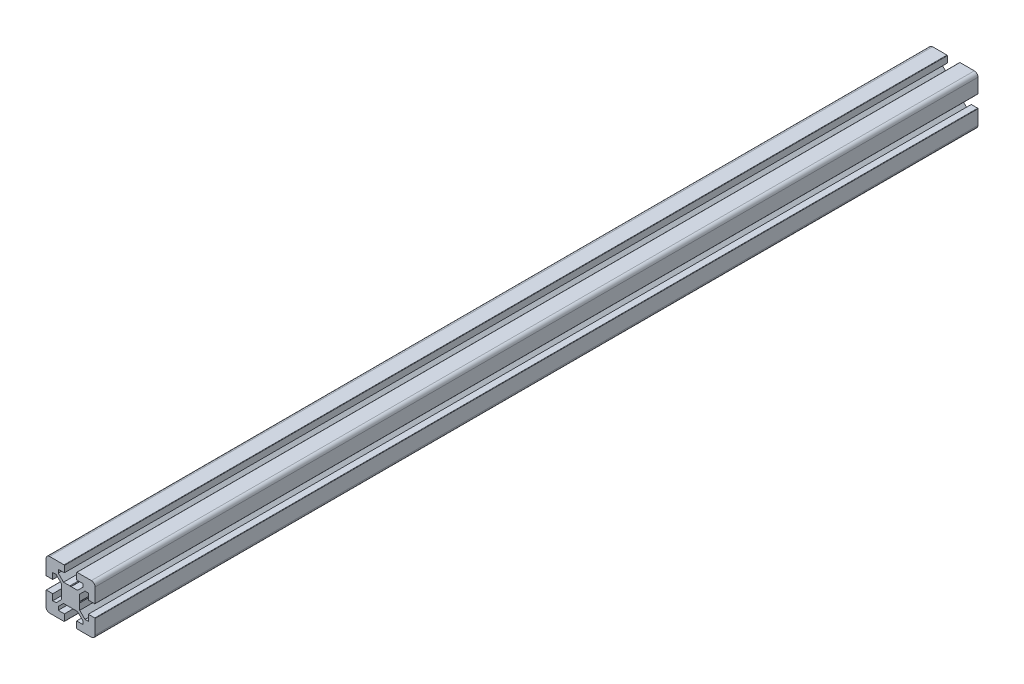
SolidWorks part; units mm, degrees
ref_plane "正面" through (0, 0, 0) normal (0, 0, 1) x (1, 0, 0)
ref_plane "平面" through (0, 0, 0) normal (0, 1, 0) x (1, 0, 0)
ref_plane "右側面" through (0, 0, 0) normal (1, 0, 0) x (0, 0, -1)
sketch "Model" plane through (0, 0, 0) normal (0, 0, 1) x (1, 0, 0)
  line L0 (160, 30) -> (160, 70)
  line L1 (110, 70) -> (110, 30)
  line L2 (160, 30) -> (110, 30)
  line L3 (110, 55) -> (160, 55)
  line L4 (110, 45) -> (160, 45)
  line L5 (160, 70) -> (110, 70)
  line L6 (105, 50) -> (165, 50) construction
  line L7 (110, 50.5196) -> (160, 50.5196)
  line L8 (110, 49.4804) -> (160, 49.4804)
  line L9 (110, 60) -> (160, 60) construction
  line L10 (110, 40) -> (160, 40) construction
  line L11 (37, 68) -> (33, 68)
  line L12 (69.7, 55) -> (64.5, 55)
  line L13 (64.5, 60) -> (64.5, 55)
  line L14 (70, 67) -> (70, 55.3)
  line L15 (68, 67) -> (68, 63)
  line L16 (64.5, 40) -> (64.5, 45)
  line L17 (69.7, 45) -> (64.5, 45)
  line L18 (70, 33) -> (70, 44.7)
  line L19 (68, 33) -> (68, 37)
  line L20 (33, 70) -> (44.7, 70)
  line L21 (60, 64.5) -> (60, 61.7678)
  line L22 (60, 64.5) -> (55, 64.5)
  line L23 (60, 61.7678) -> (55.7322, 57.5)
  line L24 (61.7678, 60) -> (57.5, 55.7322)
  line L25 (40, 64.5) -> (40, 61.7678)
  line L26 (40, 64.5) -> (45, 64.5)
  line L27 (40, 61.7678) -> (44.2678, 57.5)
  line L28 (35.5, 60) -> (38.2322, 60)
  line L29 (30.3, 55) -> (35.5, 55)
  line L30 (38.2322, 60) -> (42.5, 55.7322)
  line L31 (35.5, 55) -> (35.5, 60)
  line L32 (30, 67) -> (30, 55.3)
  line L33 (32, 67) -> (32, 63)
  line L34 (38, 67) -> (38, 63)
  line L35 (45, 69.7) -> (45, 64.5)
  line L36 (55, 69.7) -> (55, 64.5)
  line L37 (62, 67) -> (62, 63)
  line L38 (61.7678, 40) -> (57.5, 44.2678)
  line L39 (60, 35.5) -> (60, 38.2322)
  line L40 (60, 38.2322) -> (55.7322, 42.5)
  line L41 (55, 30.3) -> (55, 35.5)
  line L42 (62, 33) -> (62, 37)
  line L43 (38.2322, 40) -> (42.5, 44.2678)
  line L44 (40, 35.5) -> (40, 38.2322)
  line L45 (40, 35.5) -> (45, 35.5)
  line L46 (44.2678, 42.5) -> (49.4804, 42.5)
  line L47 (40, 38.2322) -> (44.2678, 42.5)
  line L48 (35.5, 45) -> (35.5, 40)
  line L49 (30.3, 45) -> (35.5, 45)
  line L50 (33, 38) -> (37, 38)
  line L51 (35.5, 40) -> (38.2322, 40)
  line L52 (33, 32) -> (37, 32)
  line L53 (33, 30) -> (44.7, 30)
  line L54 (30, 33) -> (30, 44.7)
  line L55 (32, 33) -> (32, 37)
  line L56 (38, 33) -> (38, 37)
  line L57 (45, 30.3) -> (45, 35.5)
  line L58 (50, 75) -> (50, 25) construction
  line L59 (57.5, 55.7322) -> (57.5, 50.5196)
  line L60 (67, 38) -> (63, 38)
  line L61 (25, 50) -> (75, 50) construction
  line L62 (64.5, 40) -> (61.7678, 40)
  line L63 (67, 62) -> (63, 62)
  line L64 (64.5, 60) -> (61.7678, 60)
  line L65 (42.5, 44.2678) -> (42.5, 49.4804)
  line L66 (37, 62) -> (33, 62)
  line L67 (44.2678, 57.5) -> (49.4804, 57.5)
  line L68 (57.5, 49.4804) -> (57.5, 44.2678)
  line L69 (42.5, 50.5196) -> (42.5, 55.7322)
  line L70 (50.5196, 57.5) -> (55.7322, 57.5)
  line L71 (55.3, 70) -> (67, 70)
  line L72 (63, 68) -> (67, 68)
  line L73 (55.3, 30) -> (67, 30)
  line L74 (63, 32) -> (67, 32)
  line L75 (55, 35.5) -> (60, 35.5)
  line L76 (50.5196, 42.5) -> (55.7322, 42.5)
  line L77 (57.2, 50) -> (57.5, 50.5196)
  line L78 (57.2, 50) -> (57.5, 49.4804)
  line L79 (42.8, 50) -> (42.5, 50.5196)
  line L80 (42.8, 50) -> (42.5, 49.4804)
  line L81 (50, 57.2) -> (49.4804, 57.5)
  line L82 (50, 57.2) -> (50.5196, 57.5)
  line L83 (50, 42.8) -> (49.4804, 42.5)
  line L84 (50, 42.8) -> (50.5196, 42.5)
  arc A0 (69.7, 55) -> (70, 55.3) centre (69.7, 55.3) ccw
  arc A1 (68, 67) -> (67, 68) centre (67, 67) ccw
  arc A2 (70, 44.7) -> (69.7, 45) centre (69.7, 44.7) ccw
  arc A3 (68, 37) -> (67, 38) centre (67, 37) ccw
  arc A4 (62, 63) -> (63, 62) centre (63, 63) ccw
  arc A5 (30, 55.3) -> (30.3, 55) centre (30.3, 55.3) ccw
  arc A6 (37, 62) -> (38, 63) centre (37, 63) ccw
  arc A7 (38, 67) -> (37, 68) centre (37, 67) ccw
  arc A8 (62, 33) -> (63, 32) centre (63, 33) ccw
  arc A9 (30.3, 45) -> (30, 44.7) centre (30.3, 44.7) ccw
  arc A10 (38, 37) -> (37, 38) centre (37, 37) ccw
  arc A11 (32, 33) -> (33, 32) centre (33, 33) ccw
  arc A12 (37, 32) -> (38, 33) centre (37, 33) ccw
  arc A13 (33, 38) -> (32, 37) centre (33, 37) ccw
  arc A14 (63, 38) -> (62, 37) centre (63, 37) ccw
  arc A15 (67, 62) -> (68, 63) centre (67, 63) ccw
  arc A16 (30, 33) -> (33, 30) centre (33, 33) ccw
  arc A17 (44.7, 30) -> (45, 30.3) centre (44.7, 30.3) ccw
  arc A18 (32, 63) -> (33, 62) centre (33, 63) ccw
  arc A19 (33, 68) -> (32, 67) centre (33, 67) ccw
  arc A20 (45, 69.7) -> (44.7, 70) centre (44.7, 69.7) ccw
  arc A21 (33, 70) -> (30, 67) centre (33, 67) ccw
  arc A22 (63, 68) -> (62, 67) centre (63, 67) ccw
  arc A23 (67, 32) -> (68, 33) centre (67, 33) ccw
  arc A24 (55, 30.3) -> (55.3, 30) centre (55.3, 30.3) ccw
  arc A25 (55.3, 70) -> (55, 69.7) centre (55.3, 69.7) ccw
  arc A26 (67, 30) -> (70, 33) centre (67, 33) ccw
  arc A27 (70, 67) -> (67, 70) centre (67, 67) ccw
  arc A28 (45.694, 53.0035) -> (45.694, 46.9966) centre (50, 50) ccw
  arc A29 (46.9981, 45.6929) -> (53.0039, 45.6943) centre (50, 50) ccw
  arc A30 (54.3061, 46.9967) -> (54.3061, 53.0034) centre (50, 50) ccw
  arc A31 (53.0033, 54.3061) -> (46.9968, 54.3062) centre (50, 50) ccw
  arc A32 (46.4038, 54.6058) -> (45.3944, 53.5962) centre (45.4038, 54.5962) ccw
  arc A33 (54.608, 53.5963) -> (53.5962, 54.6065) centre (54.5962, 54.5962) ccw
  arc A34 (53.5962, 45.3942) -> (54.6061, 46.4038) centre (54.5962, 45.4038) ccw
  arc A35 (45.3939, 46.4037) -> (46.4038, 45.3942) centre (45.4038, 45.4038) ccw
  arc A36 (45.694, 53.0035) -> (45.3944, 53.5962) centre (45.3778, 53.2158) ccw
  arc A37 (46.4038, 54.6058) -> (46.9968, 54.3062) centre (46.7842, 54.6222) ccw
  arc A38 (54.608, 53.5963) -> (54.3061, 53.0034) centre (54.6221, 53.2158) ccw
  arc A39 (53.0033, 54.3061) -> (53.5962, 54.6065) centre (53.2158, 54.6221) ccw
  arc A40 (45.3939, 46.4037) -> (45.694, 46.9966) centre (45.3778, 46.7842) ccw
  arc A41 (46.9981, 45.6929) -> (46.4038, 45.3942) centre (46.7842, 45.3779) ccw
  arc A42 (54.3061, 46.9967) -> (54.6061, 46.4038) centre (54.6222, 46.7842) ccw
  arc A43 (53.5962, 45.3942) -> (53.0039, 45.6943) centre (53.2158, 45.3778) ccw
  text T0 "HFS84040" font "SWTXT" height 4
  text T1 "HFS8-4040-50" font "SWTXT" height 4
extrude "ﾎﾞｽ - 押し出し1" add sketch "Model" against normal blind 720 contours L20 A20 L35 L26 L25 L27 L67 L81 L82 L70 L23 L21 L22 L36 A25 L71 A27 L14 A0 L12 L13 L64 L24 L59 L77 L78 L68 L38 L62 L16 L17 A2 L18 A26 L73 A24 L41 L75 L39 L40 L76 L84 L83 L46 L47 L44 L45 L57 A17 L53 A16 L54 A9 L49 L48 L51 L43 L65 L80 L79 L69 L30 L28 L31 L29 A5 L32 A21
